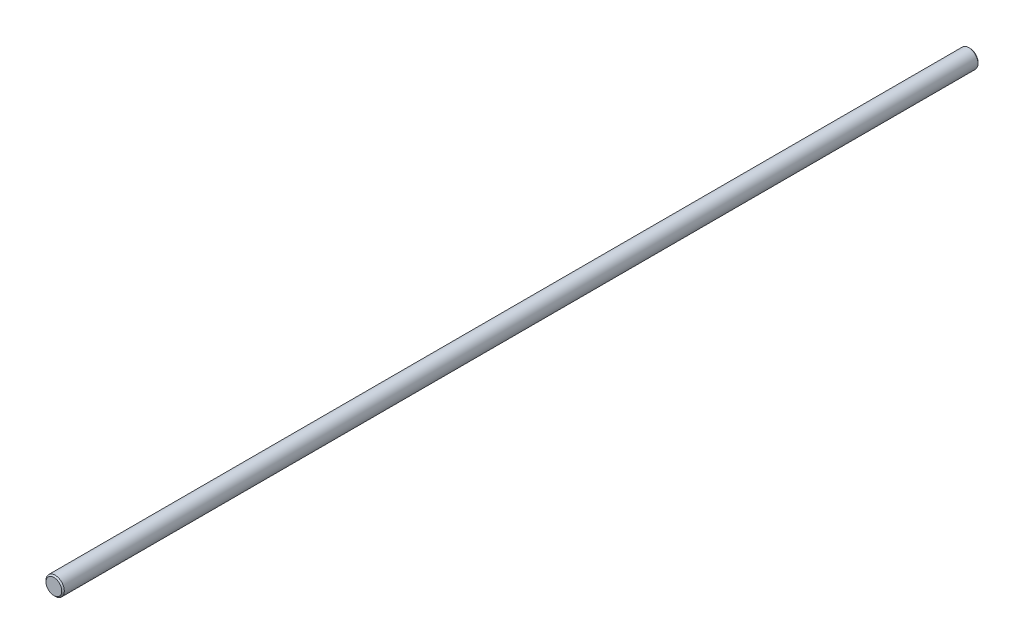
SolidWorks part; units mm, degrees
ref_plane "Front Plane" through (0, 0, 0) normal (0, 0, 1) x (1, 0, 0)
ref_plane "Top Plane" through (0, 0, 0) normal (0, 1, 0) x (1, 0, 0)
ref_plane "Right Plane" through (0, 0, 0) normal (1, 0, 0) x (0, 0, -1)
sketch "Sketch1" plane through (0, 0, 0) normal (0, 0, 1) x (1, 0, 0)
  line L0 (-3, 0) -> (3, 0) construction
  line L5 (0, 3) -> (0, -3) construction
  circle A1 centre (0, 0) radius 3
  point P7 (-3, 0)
  point P8 (3, 0)
  point P12 (0, -3)
  point P13 (0, 3)
  dimension "Diameter" = 6
sketch "Sketch2" plane through (0, 0, 0) normal (1, 0, 0) x (0, 0, -1)
  line L0 (-144, -3) -> (-144, 3) construction
  line L1 (150, -3) -> (-150, -3)
  line L2 (150, -3) -> (150, 3)
  line L3 (150, 3) -> (-150, 3)
  line L4 (-150, -3) -> (-150, 3)
  line L5 (150, -3) -> (-150, 3) construction
  line L6 (150, 3) -> (-150, -3) construction
  line L7 (144, -3) -> (144, 3) construction
  line L8 (-150, 2.58) -> (-149.58, 3) construction
  point P0 (0, 0)
  point P8 (-150, 3)
  point P9 (150, 3)
  point P14 (-144, 3)
  point P15 (-144, -3)
  point P16 (144, 3)
  point P17 (144, -3)
  point P25 (0, -3)
  dimension "Length" = 300
  dimension "D1" = 6
  dimension "D2" = 6
  dimension "Chamfer Typ," = 45
  dimension "D4" = 0.42
sketch "Sketch3" plane through (0, 0, 0) normal (0, 0, 1) x (1, 0, 0)
  circle A0 centre (0, 0) radius 3 construction
  circle A1 centre (0, 0) radius 3
extrude "Boss-Extrude1" add sketch "Sketch3" along normal up to vertex (150 mm away) and the other way up to vertex (150 mm away) up to point (0, 3, 150) other way up to point (0, 3, -150)
chamfer "Chamfer1" distance 0.42 angle 45 2 edges at (3, 0, -150) (3, 0, 150)
equation "\"D1@Sketch2\"=\"Diameter@Sketch1\""
equation "\"D2@Sketch2\"=\"Diameter@Sketch1\""
equation "\"D1@Chamfer1\"=\"Diameter@Sketch1\"*.07"
equation "\"D4@Sketch2\"=\"Diameter@Sketch1\"*.07"
equation "\"D2@Chamfer1\"=\"Chamfer Typ,@Sketch2\""
